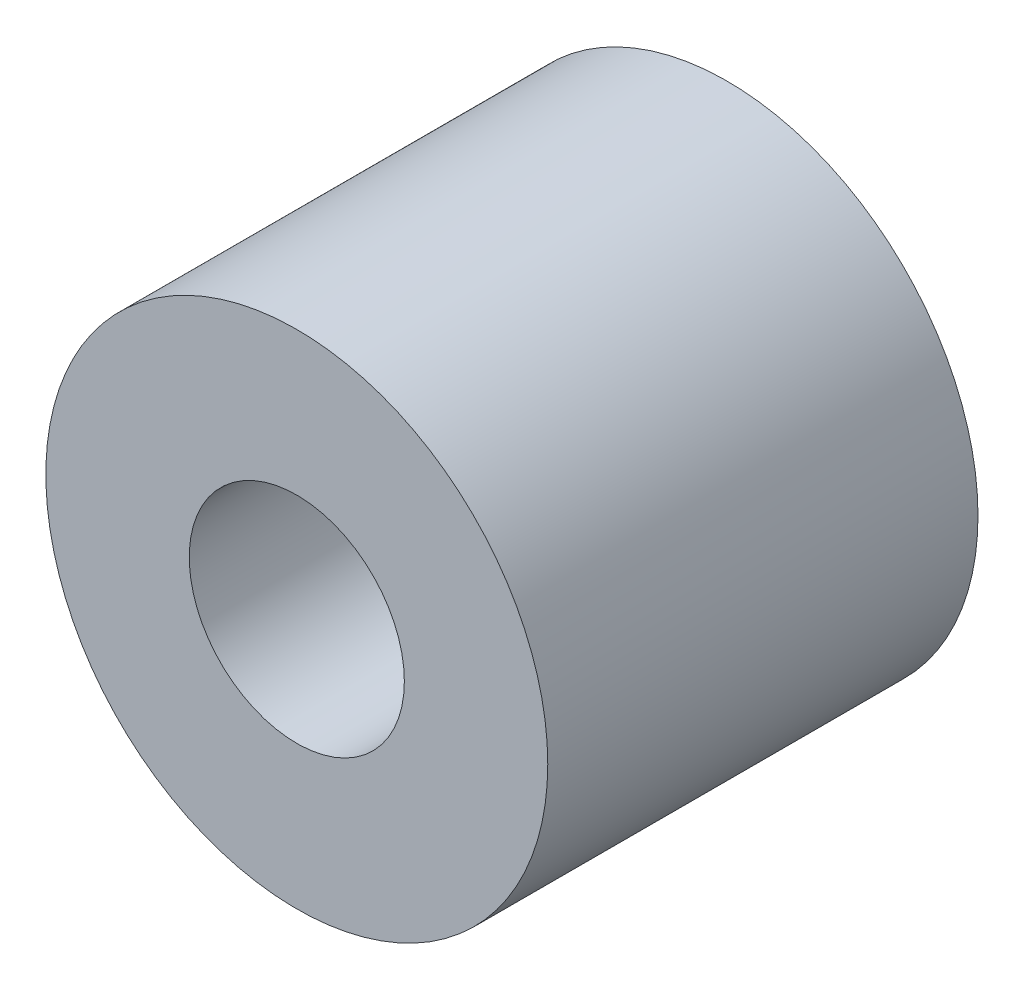
SolidWorks part; units mm, degrees
ref_plane "Front Plane" through (0, 0, 0) normal (0, 0, 1) x (1, 0, 0)
ref_plane "Top Plane" through (0, 0, 0) normal (0, 1, 0) x (1, 0, 0)
ref_plane "Right Plane" through (0, 0, 0) normal (1, 0, 0) x (0, 0, -1)
sketch "Sketch1" plane through (0, 0, 0) normal (0, 0, 1) x (1, 0, 0)
  circle A0 centre (0, 0) radius 2.7781
  circle A1 centre (0, 0) radius 1.1906
  dimension "D1" = 5.5562
  dimension "D2" = 2.3813
extrude "Boss-Extrude1" add sketch "Sketch1" along normal blind 4.7625
